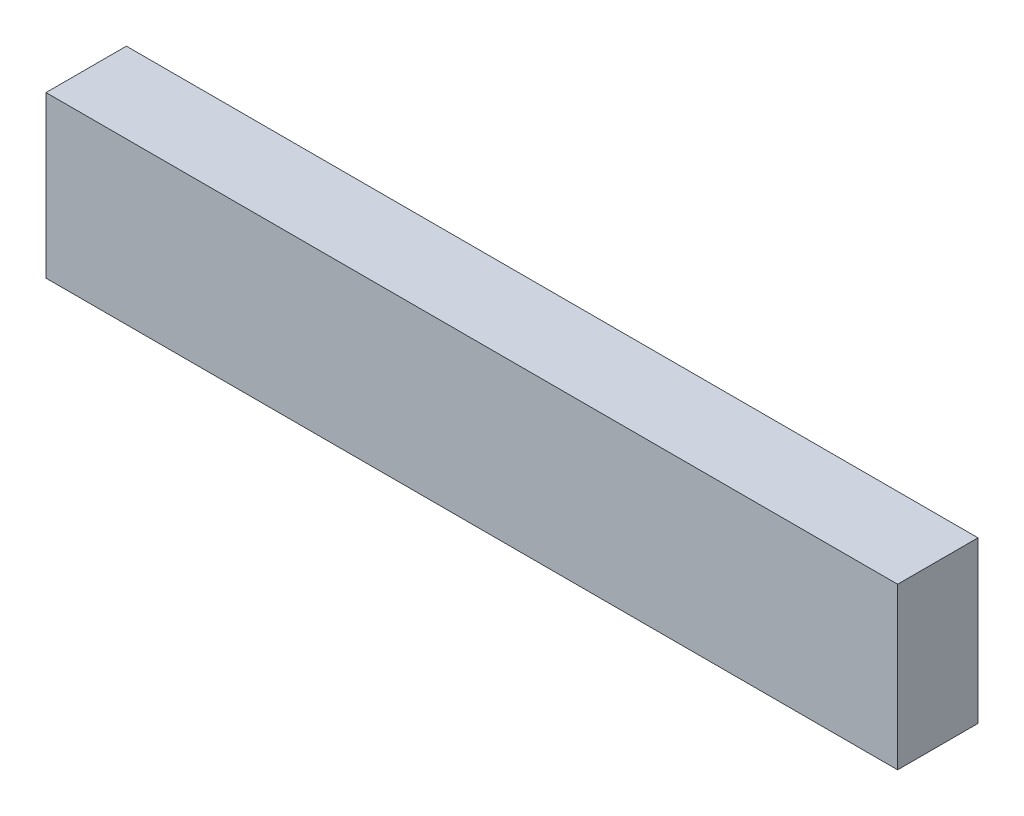
SolidWorks part; units mm, degrees
material "Cedar"
ref_plane "Front Plane" through (0, 0, 0) normal (0, 0, 1) x (1, 0, 0)
ref_plane "Top Plane" through (0, 0, 0) normal (0, 1, 0) x (1, 0, 0)
ref_plane "Right Plane" through (0, 0, 0) normal (1, 0, 0) x (0, 0, -1)
sketch "Sketch3" plane through (0, 0, 0) normal (0, 0, 1) x (1, 0, 0)
  line L1 (-25.649, 21.4157) -> (176.1794, 21.4157)
  line L2 (-25.649, 21.4157) -> (-25.649, -16.6843)
  line L3 (-25.649, -16.6843) -> (176.1794, -16.6843)
  line L4 (176.1794, 21.4157) -> (176.1794, -16.6843)
  dimension "D1" = 38.1
  dimension "D2" = 201.8284
extrude "Boss-Extrude1" add sketch "Sketch3" along normal blind 19.05
